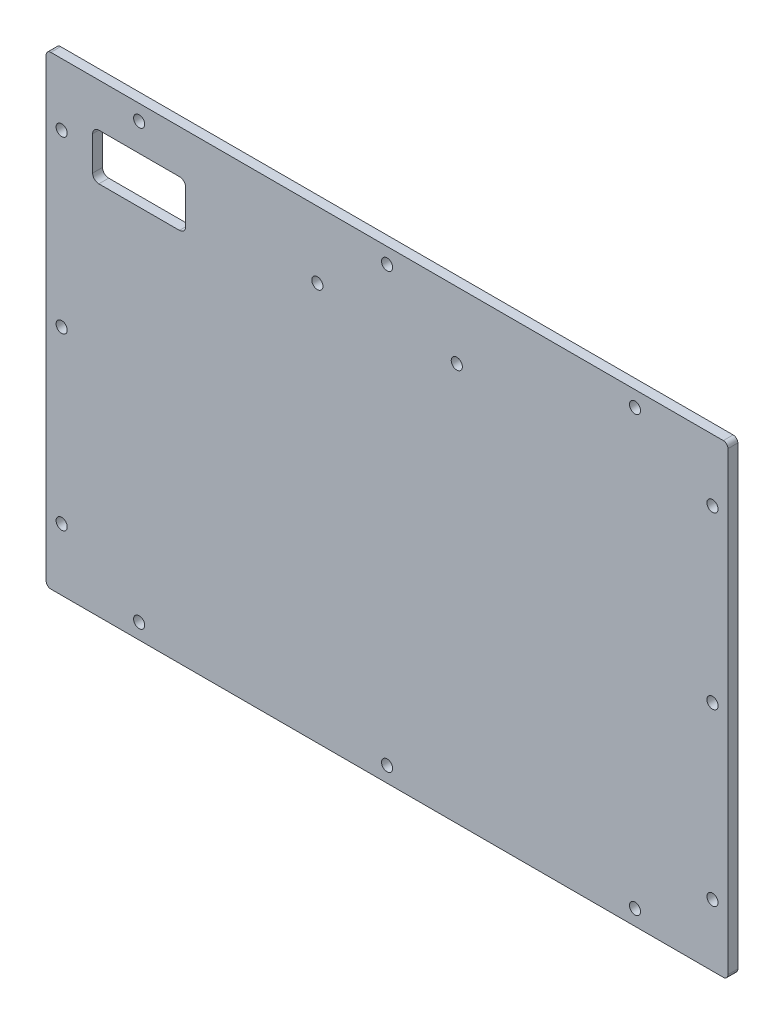
SolidWorks part; units mm, degrees
ref_plane "Front Plane" through (0, 0, 0) normal (0, 0, 1) x (1, 0, 0)
ref_plane "Top Plane" through (0, 0, 0) normal (0, 1, 0) x (1, 0, 0)
ref_plane "Right Plane" through (0, 0, 0) normal (1, 0, 0) x (0, 0, -1)
sketch "Sketch1" plane through (0, 0, 0) normal (0, 0, 1) x (1, 0, 0)
  line L0 (0, 0) -> (0, 75) construction
  line L1 (-110, -75) -> (110, -75)
  line L2 (-110, -75) -> (-110, 75)
  line L3 (-110, 75) -> (110, 75)
  line L4 (110, -75) -> (110, 75)
  line L5 (-110, -75) -> (110, 75) construction
  line L6 (-110, 75) -> (110, -75) construction
  line L15 (0, 0) -> (-110, 0) construction
  point P0 (0, 0)
  dimension "D1" = 220
  dimension "D2" = 150
extrude "Boss-Extrude1" add sketch "Sketch1" along normal blind 3.175
hole_wizard "M3 Clearance Hole1" positions "Sketch2" profile "Sketch3" hole size "M3" standard "ANSI Metric" end condition through all
sketch "Sketch2" plane through (0, 0, 3.175) normal (0, 0, 1) x (1, 0, 0)
  line L1 (-105, -70) -> (105, -70)
  line L2 (-105, -70) -> (-105, 70)
  line L3 (-105, 70) -> (105, 70)
  line L4 (105, -70) -> (105, 70)
  line L5 (-105, -70) -> (105, 70) construction
  line L6 (-105, 70) -> (105, -70) construction
  line L7 (-110, -75) -> (-110, 75) construction
  line L8 (-110, 75) -> (110, 75) construction
  point P2 (0, 0)
  point P113 (-80, 70)
  point P115 (80, 70)
  point P116 (0, 70)
  point P118 (-105, 55)
  point P120 (-105, 0)
  point P122 (-105, -55)
  point P124 (-80, -70)
  point P126 (0, -70)
  point P128 (80, -70)
  point P130 (105, -55)
  point P132 (105, 0)
  point P134 (105, 55)
  dimension "D1" = 5
  dimension "D2" = 5
  dimension "D3" = 80
  dimension "D4" = 80
  dimension "D5" = 55
  dimension "D6" = 55
sketch "Sketch3" plane through (0, 0, 3.175) normal (1, 0, 0) x (0, -1, 0)
  line L0 (0, 0) -> (0, 3.175)
  line L1 (0, 3.175) -> (1.8, 3.175)
  line L2 (1.8, 3.175) -> (1.8, 0)
  line L5 (1.8, 0) -> (0, 0)
  line L11 (0, -6.35) -> (0, 107.95) construction
  dimension "Thru Hole Dia." = 3.6
  dimension "Thru Hole Depth" = 3.175
sketch "Sketch4" plane through (0, 0, 3.175) normal (0, 0, 1) x (1, 0, 0)
  line L1 (-5, -5) -> (5, -5)
  line L2 (-5, -5) -> (-5, 5)
  line L3 (-5, 5) -> (5, 5)
  line L4 (5, -5) -> (5, 5)
  line L5 (-5, -5) -> (5, 5) construction
  line L6 (-5, 5) -> (5, -5) construction
  point P0 (0, 0)
  dimension "D1" = 10
  dimension "D2" = 10
extrude "Boss-Extrude2" add sketch "Sketch4" against normal through all
fillet "Fillet2" radius 1.5 4 edges at (-110, -75, 1.5875) (110, -75, 1.5875) (110, 75, 1.5875) (-110, 75, 1.5875)
sketch "Sketch7" plane through (0, 0, 3.175) normal (0, 0, 1) x (1, 0, 0)
  line L8 (-100, -65) -> (100, -65)
  line L9 (-100, 65) -> (-100, -65)
  line L10 (100, 65) -> (-100, 65)
  line L11 (100, -65) -> (100, 65)
  line L12 (-100, -65) -> (100, -65) construction
  line L13 (-100, 65) -> (-100, -65) construction
  line L14 (100, 65) -> (-100, 65) construction
  line L15 (100, -65) -> (100, 65) construction
  line L20 (-22.5, 53.5) -> (22.5, 53.5) construction
  line L22 (-49.5, 42) -> (49.5, 42) construction
  line L23 (-49.5, 42) -> (-49.5, 65) construction
  line L24 (-49.5, 65) -> (49.5, 65) construction
  line L25 (49.5, 42) -> (49.5, 65) construction
  line L26 (-49.5, 42) -> (49.5, 65) construction
  line L27 (-49.5, 65) -> (49.5, 42) construction
  line L29 (-95, 46) -> (-65, 46)
  line L30 (-95, 46) -> (-95, 61)
  line L31 (-95, 61) -> (-65, 61)
  line L32 (-65, 46) -> (-65, 61)
  line L33 (-95, 46) -> (-65, 61) construction
  line L34 (-95, 61) -> (-65, 46) construction
  point P1 (0, 65)
  point P66 (-22.5, 53.5)
  point P67 (22.5, 53.5)
  point P76 (0, 53.5)
  point P138 (-80, 53.5)
  dimension "D2" = 45
  dimension "D3" = 99
  dimension "D4" = 23
  dimension "D5" = 15
  dimension "D6" = 30
  dimension "D7" = 5
  dimension "D1" = 10
extrude "Cut-Extrude2" cut sketch "Sketch7" against normal through all
hole_wizard "M3 Clearance Hole3" positions "Sketch8" profile "Sketch9" hole size "M3" standard "ANSI Metric" end condition through all
sketch "Sketch8" plane through (0, 0, 3.175) normal (0, 0, 1) x (1, 0, 0)
  point P0 (-22.5, 53.5)
  point P3 (22.5, 53.5)
sketch "Sketch9" plane through (-22.5, 53.5, 3.175) normal (1, 0, 0) x (0, -1, 0)
  line L0 (0, 0) -> (0, 3.175)
  line L1 (0, 3.175) -> (1.8, 3.175)
  line L2 (1.8, 3.175) -> (1.8, 0)
  line L5 (1.8, 0) -> (0, 0)
  line L11 (0, -6.35) -> (0, 107.95) construction
  dimension "Thru Hole Dia." = 3.6
  dimension "Thru Hole Depth" = 3.175
fillet "Fillet3" radius 2 4 edges at (-95, 61, 1.5875) (-95, 46, 1.5875) (-65, 46, 1.5875) (-65, 61, 1.5875)
